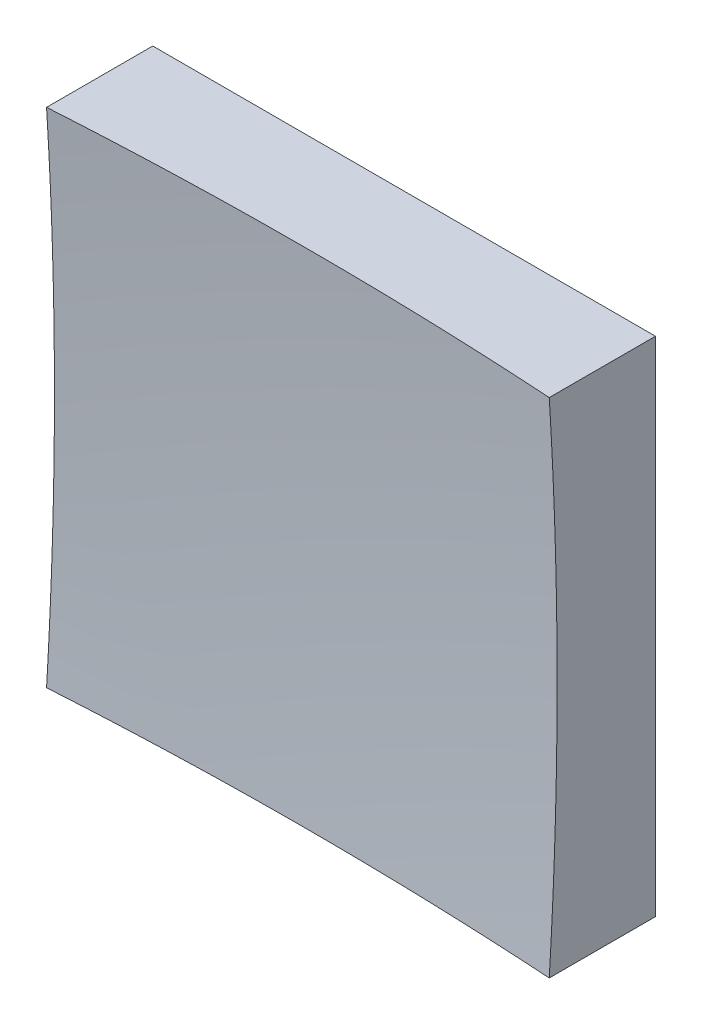
SolidWorks part; units mm, degrees
ref_plane "前视基准面" through (0, 0, 0) normal (0, 0, 1) x (1, 0, 0)
ref_plane "上视基准面" through (0, 0, 0) normal (0, 1, 0) x (1, 0, 0)
ref_plane "右视基准面" through (0, 0, 0) normal (1, 0, 0) x (0, 0, -1)
sketch "草图1" plane through (0, 0, 0) normal (0, 0, 1) x (1, 0, 0)
  line L1 (-25, 25) -> (25, 25)
  line L2 (-25, 25) -> (-25, -25)
  line L3 (-25, -25) -> (25, -25)
  line L4 (25, 25) -> (25, -25)
  line L5 (-25, 25) -> (25, -25) construction
  line L6 (-25, -25) -> (25, 25) construction
  point P0 (0, 0)
  dimension "D1" = 50
  dimension "D2" = 50
extrude "凸台-拉伸1" add sketch "草图1" along normal blind 50 contours L2 L3 L4 L1
sketch "草图2" plane through (0, 0, 0) normal (0, 1, 0) x (1, 0, 0)
  line L0 (-7.4603, -9) -> (7.3192, -9) construction
  line L1 (0, 0) -> (0, -12.1749) construction
  line L2 (389.9382, -319.8473) -> (0, -319.8473)
  line L3 (0, -319.8473) -> (0, -9)
  arc A1 (389.9382, -319.8473) -> (0, -9) centre (0, -409) ccw
  dimension "D2" = 800
  dimension "D1" = 9
revolve "切除-旋转2" cut sketch "草图2" angle 360 about L3
